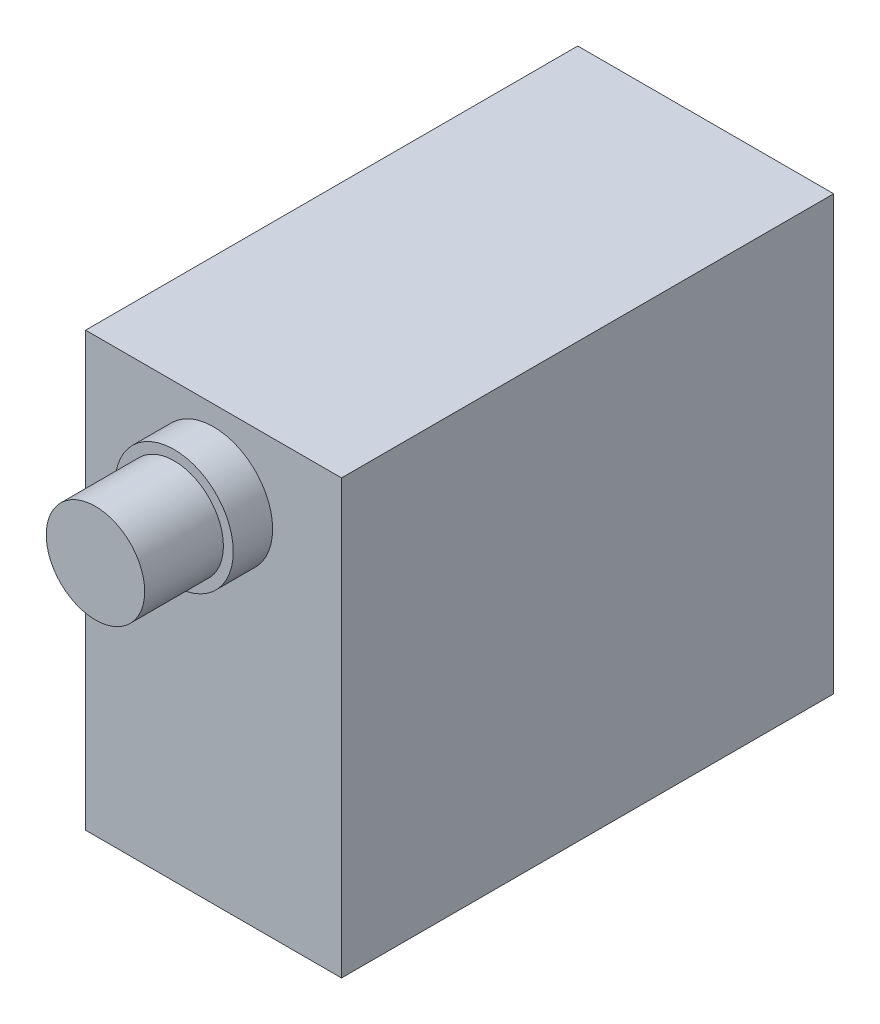
SolidWorks part; units mm, degrees
ref_plane "Front Plane" through (0, 0, 0) normal (0, 0, 1) x (1, 0, 0)
ref_plane "Top Plane" through (0, 0, 0) normal (0, 1, 0) x (1, 0, 0)
ref_plane "Right Plane" through (0, 0, 0) normal (1, 0, 0) x (0, 0, -1)
sketch "Sketch1" plane through (0, 0, 0) normal (0, 0, 1) x (1, 0, 0)
  line L1 (6.5, -11) -> (-6.5, -11)
  line L2 (6.5, -11) -> (6.5, 11)
  line L3 (6.5, 11) -> (-6.5, 11)
  line L4 (-6.5, -11) -> (-6.5, 11)
  line L5 (6.5, -11) -> (-6.5, 11) construction
  line L6 (6.5, 11) -> (-6.5, -11) construction
  point P0 (0, 0)
  dimension "D1" = 13
  dimension "D2" = 22
extrude "Boss-Extrude1" add sketch "Sketch1" along normal blind 25
sketch "Sketch2" plane through (0, 0, 25) normal (0, 0, 1) x (1, 0, 0)
  line L0 (6.5, 11) -> (-6.5, 11) construction
  circle A1 centre (0, 7) radius 3
  dimension "D3" = 6
  dimension "D2" = 4
extrude "Boss-Extrude2" add sketch "Sketch2" along normal blind 2
sketch "Sketch3" plane through (0, 0, 27) normal (0, 0, 1) x (1, 0, 0)
  circle A0 centre (0, 7) radius 2.5
  circle A1 centre (0, 7) radius 3 construction
  dimension "D1" = 5
extrude "Boss-Extrude3" add sketch "Sketch3" along normal blind 4
